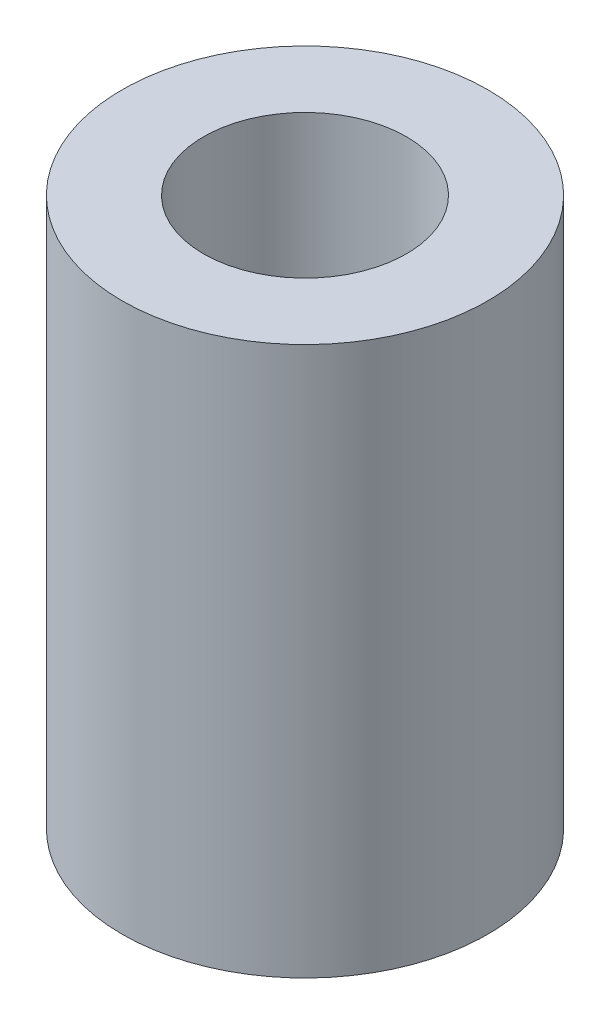
SolidWorks part; units mm, degrees
ref_plane "Front Plane" through (0, 0, 0) normal (0, 0, 1) x (1, 0, 0)
ref_plane "Top Plane" through (0, 0, 0) normal (0, 1, 0) x (1, 0, 0)
ref_plane "Right Plane" through (0, 0, 0) normal (1, 0, 0) x (0, 0, -1)
sketch "Sketch1" plane through (0, 0, 0) normal (0, 1, 0) x (1, 0, 0)
  circle A0 centre (0, 0) radius 10
  dimension "D1" = 20
extrude "Boss-Extrude1" add sketch "Sketch1" along normal blind 15
sketch "Sketch2" plane through (0, 0, 0) normal (0, -1, 0) x (1, 0, 0)
  circle A0 centre (0, 0) radius 5.55
  dimension "D1" = 11.1
extrude "Cut-Extrude1" cut sketch "Sketch2" against normal blind 9
sketch "Sketch3" plane through (0, 0, 0) normal (0, 0, 1) x (1, 0, 0)
  line L0 (0, 0) -> (0, 9) construction
  line L1 (-10, 0) -> (10, 0) construction
  line L9 (10, 15) -> (-10, 15) construction
  line L15 (0, 9) -> (0, 15)
  line L16 (0, 15) -> (-2.25, 15)
  line L18 (0, 15) -> (0, 15.3095)
  line L20 (-2.4309, 13.9739) -> (-4.2413, 9)
  line L21 (-4.2413, 9) -> (0, 9)
  arc A0 (-2.4309, 13.9739) -> (-2.25, 15) centre (-5.25, 15) ccw
  dimension "D3" = 6
  dimension "D1" = 9
  dimension "D2" = 70
revolve "Cut-Revolve3" cut sketch "Sketch3" angle 360 about L18
mirror "Mirror1" about plane through (0, 15, 0) normal (0, 1, 0) of "Cut-Extrude1", "Cut-Revolve3", "Boss-Extrude1"
